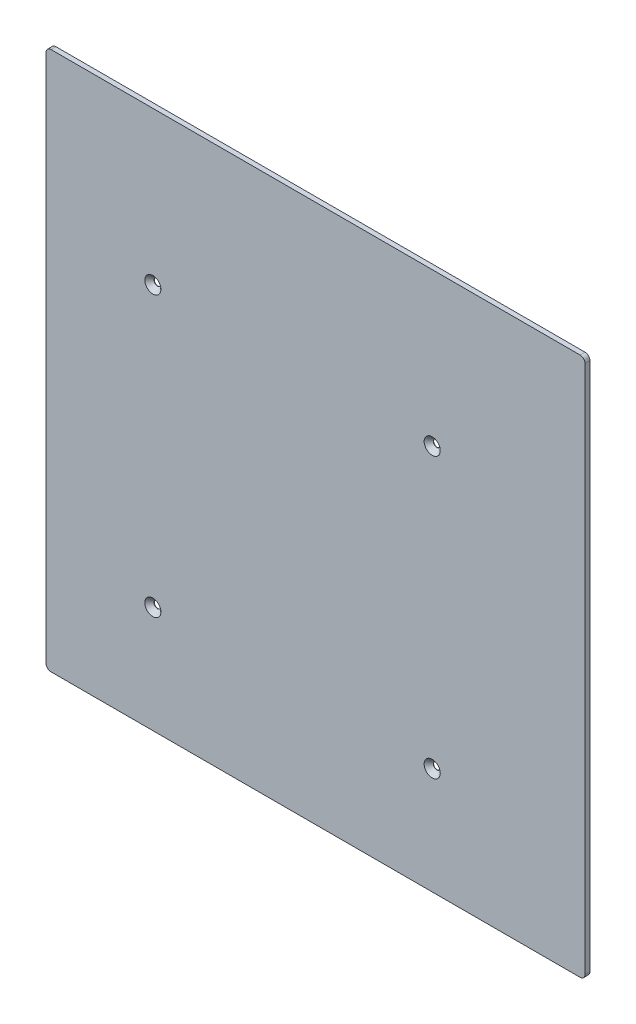
SolidWorks part; units mm, degrees
ref_plane "Front Plane" through (0, 0, 0) normal (0, 0, 1) x (1, 0, 0)
ref_plane "Top Plane" through (0, 0, 0) normal (0, 1, 0) x (1, 0, 0)
ref_plane "Right Plane" through (0, 0, 0) normal (1, 0, 0) x (0, 0, -1)
ref_plane "Plane1" through (0, 0, 0) normal (0, 0, -1) x (-1, 0, 0)
sketch "Sketch1" plane through (0, 0, 0) normal (0, 0, -1) x (-1, 0, 0)
  line L0 (150, -150) -> (150, 178)
  line L1 (150, 178) -> (-178, 178)
  line L2 (-178, 178) -> (-178, -150)
  line L3 (-178, -150) -> (150, -150)
  dimension "D1" = 328
  dimension "D2" = 328
extrude "Boss-Extrude1" add sketch "Sketch1" against normal blind 3
sketch "Sketch2" plane through (0, 0, 0) normal (0, 0, -1) x (-1, 0, 0)
  line L0 (72.6508, 117.5) -> (72.6508, 106.0508)
  line L1 (72.6508, 106.0508) -> (101.4629, 106.0508)
  line L2 (101.4629, 106.0508) -> (101.4629, 117.5)
  line L3 (101.4629, 117.5) -> (72.6508, 117.5)
extrude "Cut-Extrude1" cut sketch "Sketch2" against normal blind 0.5
hole_wizard "CSK for M3.5 Flat Head Machine Screw1" positions "Sketch4" profile "Sketch3" countersink size "M3.5" standard "ANSI Metric"
sketch "Sketch4" plane through (0, 0, 3) normal (0, 0, 1) x (1, 0, 0)
  point P0 (-85, -85)
  point P1 (85, -85)
  point P2 (85, 85)
  point P3 (-85, 85)
sketch "Sketch3" plane through (-85, -85, 3) normal (1, 0, 0) x (0, -1, 0)
  line L0 (0, 0) -> (0, 3)
  line L1 (0, 3) -> (2.1, 3)
  line L2 (2.1, 3) -> (2.1, 2.8)
  line L3 (2.1, 2.8) -> (4.9, 0)
  line L5 (4.9, 0) -> (0, 0)
  line L6 (-2.1, 2.8) -> (-4.9, 0) construction
  line L11 (0, -6.35) -> (0, 107.95) construction
  dimension "Thru Hole Dia." = 4.2
  dimension "Thru Hole Depth" = 3
  dimension "Near C'Sink Dia." = 9.8
  dimension "Near C'Sink Angle" = 90
fillet "Fillet1" radius 3 4 edges at (-150, -150, 1.5) (178, -150, 1.5) (-150, 178, 1.5) (178, 178, 1.5)
